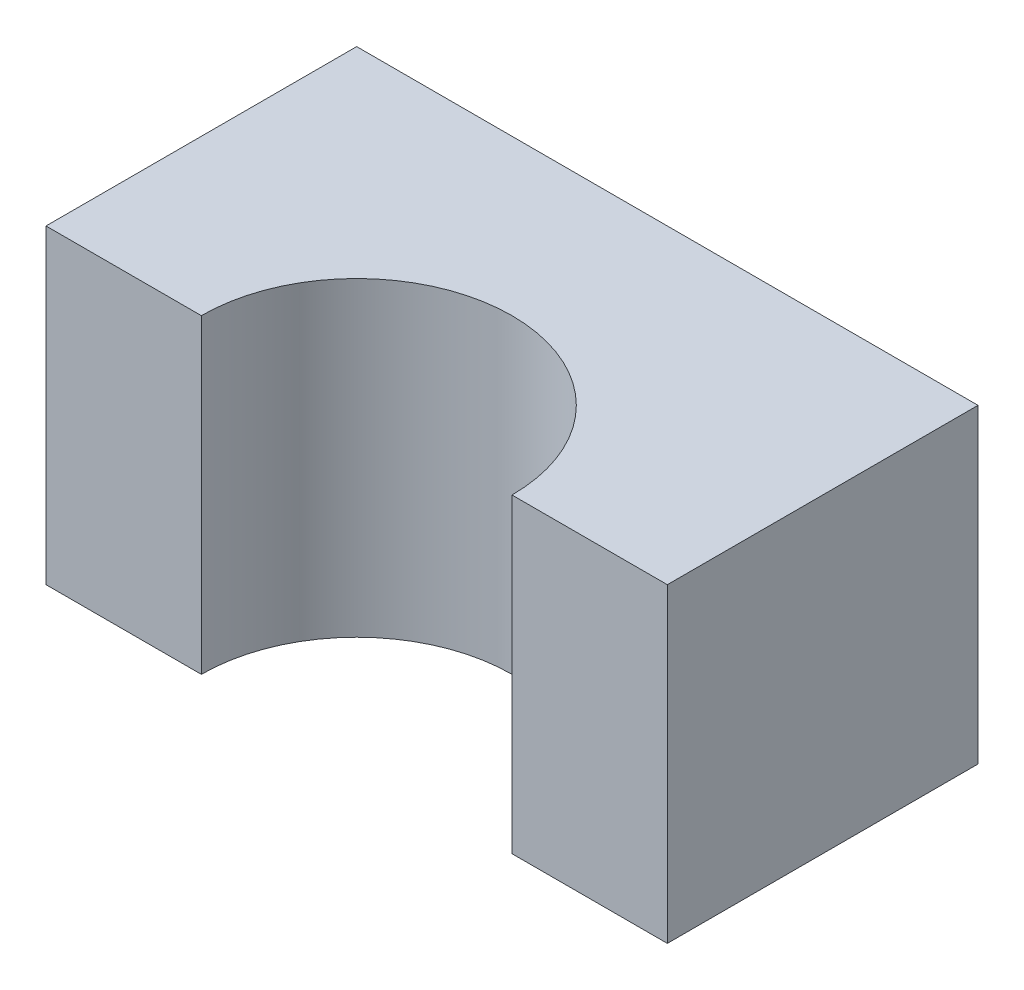
SolidWorks part; units mm, degrees
ref_plane "Alzado" through (0, 0, 0) normal (0, 0, 1) x (1, 0, 0)
ref_plane "Planta" through (0, 0, 0) normal (0, 1, 0) x (1, 0, 0)
ref_plane "Vista lateral" through (0, 0, 0) normal (1, 0, 0) x (0, 0, -1)
sketch "Croquis1" plane through (0, 0, 0) normal (0, 1, 0) x (1, 0, 0)
  line L1 (-20, 10) -> (20, 10)
  line L2 (-20, 10) -> (-20, -10)
  line L3 (-20, -10) -> (20, -10)
  line L4 (20, 10) -> (20, -10)
  line L5 (-20, 10) -> (20, -10) construction
  line L6 (-20, -10) -> (20, 10) construction
  point P0 (0, 0)
  dimension "D1" = 40
  dimension "D2" = 20
extrude "Saliente-Extruir1" add sketch "Croquis1" along normal blind 20
sketch "Croquis2" plane through (0, 20, 0) normal (0, 1, 0) x (1, 0, 0)
  line L0 (-20, -10) -> (20, -10) construction
  circle A0 centre (0, -10) radius 10
extrude "Cortar-Extruir1" cut sketch "Croquis2" against normal blind 20
